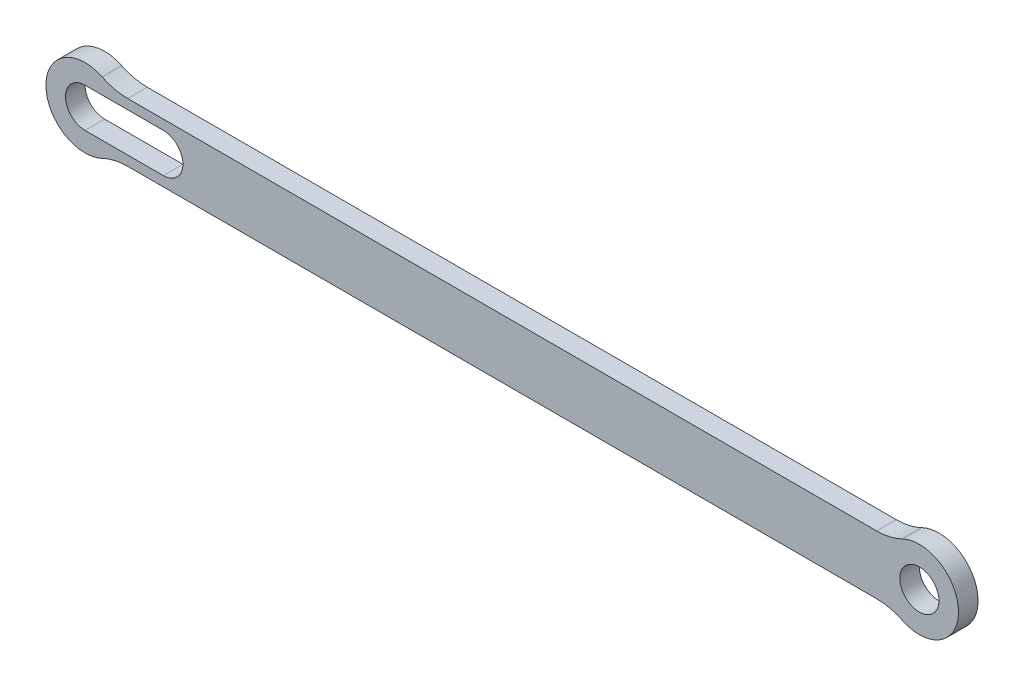
SolidWorks part; units mm, degrees
material "Brass"
ref_plane "Front Plane" through (0, 0, 0) normal (0, 0, 1) x (1, 0, 0)
ref_plane "Top Plane" through (0, 0, 0) normal (0, 1, 0) x (1, 0, 0)
ref_plane "Right Plane" through (0, 0, 0) normal (1, 0, 0) x (0, 0, -1)
sketch "Sketch1" plane through (0, 0, 0) normal (0, 0, 1) x (1, 0, 0)
  line L0 (55, 0) -> (-55, 0) construction
  line L1 (-213.13, 0) -> (-193.13, 0) construction
  line L2 (-202.2328, -7.5) -> (-10.8972, -7.5)
  line L3 (-202.2328, 7.5) -> (-10.8972, 7.5)
  line L4 (-213.13, 5) -> (-193.13, 5)
  line L5 (-213.13, -5) -> (-193.13, -5)
  arc A0 (-4.3589, -9) -> (-4.3589, 9) centre (0, 0) ccw
  circle A1 centre (0, 0) radius 5
  arc A2 (-208.7711, 9) -> (-208.7711, -9) centre (-213.13, 0) ccw
  arc A3 (-4.3589, 9) -> (-10.8972, 7.5) centre (-10.8972, 22.5) cw
  arc A4 (-4.3589, -9) -> (-10.8972, -7.5) centre (-10.8972, -22.5) ccw
  arc A5 (-208.7711, -9) -> (-202.2328, -7.5) centre (-202.2328, -22.5) cw
  arc A6 (-202.2328, 7.5) -> (-208.7711, 9) centre (-202.2328, 22.5) cw
  arc A7 (-213.13, 5) -> (-213.13, -5) centre (-213.13, 0) ccw
  arc A8 (-193.13, -5) -> (-193.13, 5) centre (-193.13, 0) ccw
  point P8 (-213.13, -7.5)
  point P9 (0, -7.5)
  point P10 (-213.13, 7.5)
  point P11 (0, 7.5)
  point P23 (-203.13, 0)
  dimension "D1" = 10
  dimension "D2" = 20
  dimension "D3" = 20
  dimension "D5" = 15
  dimension "D10" = 5
  dimension "D4" = 213.13
  dimension "D6" = 191.3355
  dimension "D7" = 191.3355
  dimension "D8" = 15
  dimension "D9" = 20
extrude "Boss-Extrude1" add sketch "Sketch1" along normal blind 5
